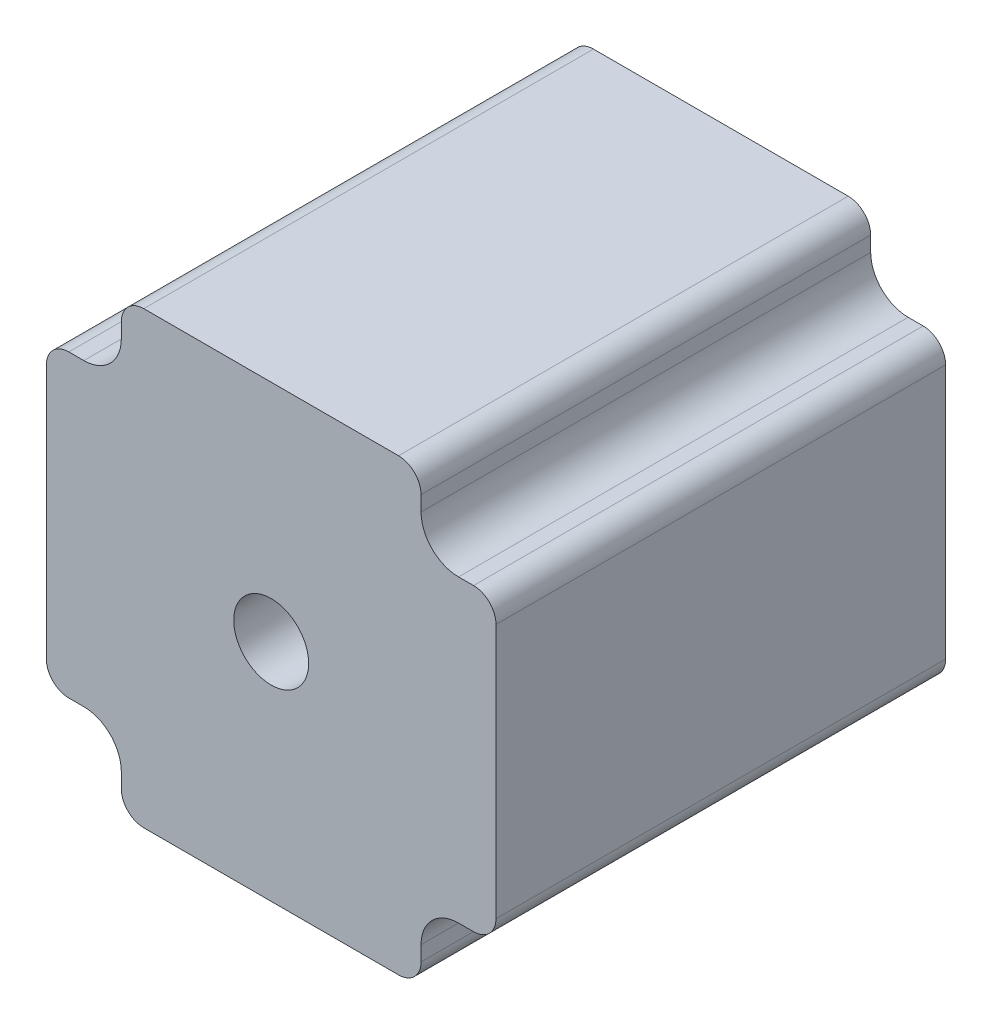
SolidWorks part; units mm, degrees
material "AISI 1020"
ref_plane "Ön Düzlem" through (0, 0, 0) normal (0, 0, 1) x (1, 0, 0)
ref_plane "Üst Düzlem" through (0, 0, 0) normal (0, 1, 0) x (1, 0, 0)
ref_plane "Sağ Düzlem" through (0, 0, 0) normal (1, 0, 0) x (0, 0, -1)
sketch "Çizim1" plane through (0, 0, 0) normal (0, 0, 1) x (1, 0, 0)
  line L0 (-45.2999, 30.7317) -> (-45.2999, 28.7317)
  line L1 (-42.2999, 33.7317) -> (-8.2999, 33.7317)
  line L2 (-55.2999, 20.7317) -> (-55.2999, -13.2683)
  line L3 (-42.2999, -26.2683) -> (-8.2999, -26.2683)
  line L4 (4.7001, 20.7317) -> (4.7001, -13.2683)
  line L5 (-50.2999, 23.7317) -> (-52.2999, 23.7317)
  line L6 (-45.2999, -23.2683) -> (-45.2999, -21.2683)
  line L7 (-50.2999, -16.2683) -> (-52.2999, -16.2683)
  line L8 (-5.2999, -23.2683) -> (-5.2999, -21.2683)
  line L9 (-0.2999, -16.2683) -> (1.7001, -16.2683)
  line L10 (1.7001, 23.7317) -> (-0.2999, 23.7317)
  line L11 (-5.2999, 28.7317) -> (-5.2999, 30.7317)
  arc A0 (-45.2999, -21.2683) -> (-50.2999, -16.2683) centre (-50.2999, -21.2683) ccw
  arc A1 (-5.2999, -21.2683) -> (-0.2999, -16.2683) centre (-0.2999, -21.2683) cw
  arc A2 (-0.2999, 23.7317) -> (-5.2999, 28.7317) centre (-0.2999, 28.7317) cw
  arc A3 (-45.2999, 28.7317) -> (-50.2999, 23.7317) centre (-50.2999, 28.7317) cw
  arc A4 (-52.2999, -16.2683) -> (-55.2999, -13.2683) centre (-52.2999, -13.2683) cw
  arc A5 (-45.2999, -23.2683) -> (-42.2999, -26.2683) centre (-42.2999, -23.2683) ccw
  arc A6 (-5.2999, -23.2683) -> (-8.2999, -26.2683) centre (-8.2999, -23.2683) cw
  arc A7 (1.7001, -16.2683) -> (4.7001, -13.2683) centre (1.7001, -13.2683) ccw
  arc A8 (1.7001, 23.7317) -> (4.7001, 20.7317) centre (1.7001, 20.7317) cw
  arc A9 (-5.2999, 30.7317) -> (-8.2999, 33.7317) centre (-8.2999, 30.7317) ccw
  arc A10 (-45.2999, 30.7317) -> (-42.2999, 33.7317) centre (-42.2999, 30.7317) cw
  arc A11 (-52.2999, 23.7317) -> (-55.2999, 20.7317) centre (-52.2999, 20.7317) ccw
  point P2 (-45.2999, -16.2683)
  point P17 (-5.2999, -16.2683)
  point P22 (-45.2999, 23.7317)
  point P27 (-45.2999, -26.2683)
  point P32 (4.7001, -16.2683)
  point P39 (-45.2999, 33.7317)
  point P42 (-55.2999, 23.7317)
  dimension "D1" = 5
  dimension "D2" = 3
  dimension "D3" = 10
  dimension "D4" = 10
  dimension "D5" = 10
  dimension "D6" = 10
extrude "Yükseklik-Ekstrüzyon1" add sketch "Çizim1" along normal blind 60
sketch "Çizim2" plane through (0, 0, 60) normal (0, 0, 1) x (1, 0, 0)
  line L0 (-55.2999, 20.7317) -> (-55.2999, -13.2683) construction
  line L2 (-8.2999, 33.7317) -> (-42.2999, 33.7317) construction
  circle A0 centre (-25.2999, 3.7317) radius 5
  dimension "D1" = 30
  dimension "D2" = 30
  dimension "D3" = 10
extrude "Kes-Ekstrüzyon1" cut sketch "Çizim2" against normal through all
